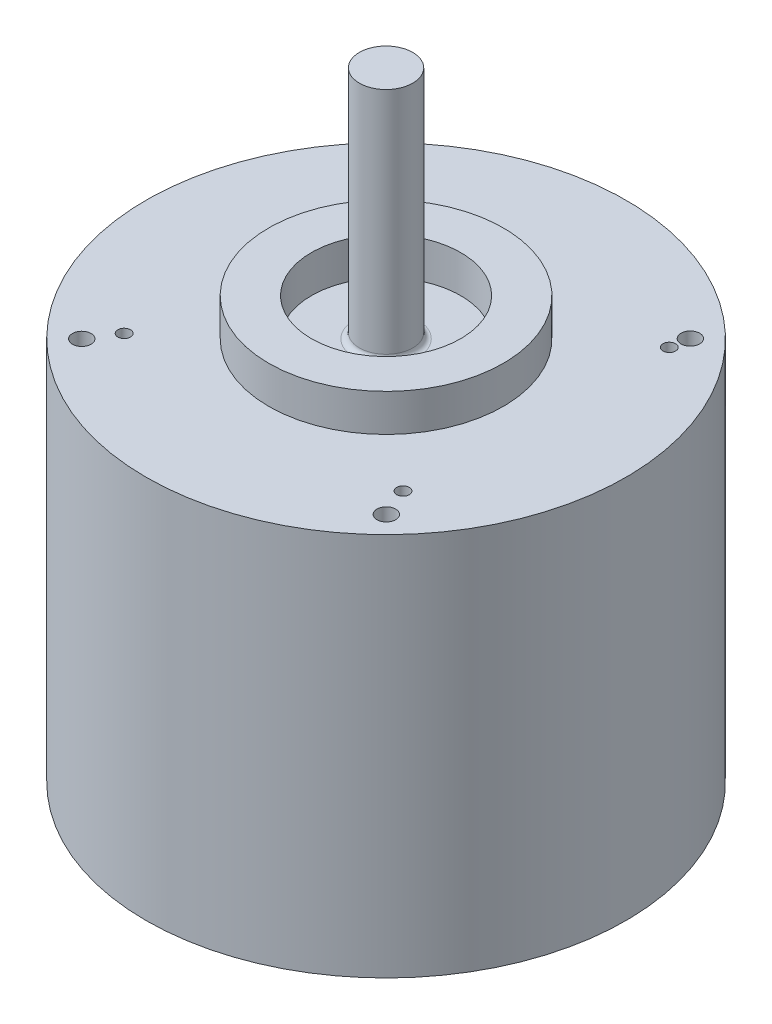
SolidWorks part; units mm, degrees
ref_plane "Front Plane" through (0, 0, 0) normal (0, 0, 1) x (1, 0, 0)
ref_plane "Top Plane" through (0, 0, 0) normal (0, 1, 0) x (1, 0, 0)
ref_plane "Right Plane" through (0, 0, 0) normal (1, 0, 0) x (0, 0, -1)
sketch "Sketch1" plane through (0, 0, 0) normal (0, 1, 0) x (1, 0, 0)
  circle A0 centre (0, 0) radius 22.5
  dimension "D1" = 45
extrude "Boss-Extrude1" add sketch "Sketch1" along normal blind 36
sketch "Sketch2" plane through (0, 36, 0) normal (0, 1, 0) x (1, 0, 0)
  circle A0 centre (0, 0) radius 11
extrude "Boss-Extrude2" add sketch "Sketch2" along normal blind 3.5
sketch "Sketch5" plane through (0, 39.5, 0) normal (0, 1, 0) x (1, 0, 0)
  circle A0 centre (0, 0) radius 7
extrude "Cut-Extrude1" cut sketch "Sketch5" against normal blind 3.5
sketch "Sketch6" plane through (0, 36, 0) normal (0, 1, 0) x (1, 0, 0)
  circle A0 centre (0, 0) radius 2.5
extrude "Boss-Extrude3" add sketch "Sketch6" along normal blind 22
fillet "Fillet1" radius 0.5 1 edges at (0, 36, 2.5)
sketch "Sketch7" plane through (0, 0, 0) normal (0, -1, 0) x (1, 0, 0)
  circle A1 centre (0, -11.5) radius 2.5
sketch "Sketch18" plane through (0, 36, 0) normal (0, 1, 0) x (1, 0, 0)
  line L1 (14.2767, -14.2534) -> (14.2534, 14.2767)
  line L2 (14.2534, 14.2767) -> (-14.2767, 14.2534)
  line L3 (-14.2767, 14.2534) -> (-14.2534, -14.2767)
  line L4 (-14.2534, -14.2767) -> (14.2767, -14.2534)
  circle A0 centre (0, 0) radius 14.265 construction
hole_wizard "M2.2x0.45 Tapped Hole1" positions "3DSketch6" profile "Sketch19" tap size "M2.2x0.45" standard "Ansi Metric"
sketch3d "3DSketch6"
  point P0 (-14.2767, 36, -14.2534)
  point P3 (14.2534, 36, -14.2767)
  point P6 (-14.2534, 36, 14.2767)
  point P9 (14.2767, 36, 14.2534)
sketch "Sketch19" plane through (-14.2767, 36, -14.2534) normal (1, 0, 0) x (0, 0, 1)
  line L0 (0, 0) -> (0, 6.2758)
  line L1 (0, 6.2758) -> (0.875, 5.75)
  line L2 (0.875, 5.75) -> (0.875, 0)
  line L5 (0.875, 0) -> (0, 0)
  line L10 (0, 6.2758) -> (-0.875, 5.75) construction
  line L11 (0, -6.35) -> (0, 107.95) construction
  dimension "Tap Drill Dia." = 1.75
  dimension "Tap Drill Depth" = 5.75
  dimension "Drill Angle" = 118
cosmetic thread "Hole Thread14" parameters "D1"=4.4, "D2"=2.2
cosmetic thread "Hole Thread15" parameters "D1"=4.4, "D2"=2.2
cosmetic thread "Hole Thread16" parameters "D1"=4.4, "D2"=2.2
cosmetic thread "Hole Thread17" parameters "D1"=4.4, "D2"=2.2
sketch "Sketch21" plane through (0, 0, 0) normal (0, -1, 0) x (1, 0, 0)
  circle A1 centre (0, -11.5) radius 2.4901
extrude "Boss-Extrude6" add sketch "Sketch21" along normal blind 7
hole_wizard "#0-80 Tapped Hole3" positions "3DSketch3" profile "Sketch14" tap size "#0-80" standard "Ansi Inch"
sketch3d "3DSketch3"
  point P0 (-13.1635, 36, -12.0288)
  point P2 (13.1635, 36, 11.5748)
  point P4 (13.9806, 36, -12.5735)
  point P6 (-12.7096, 36, 11.8472)
sketch "Sketch14" plane through (-13.1635, 36, -12.0288) normal (1, 0, 0) x (0, 0, 1)
  line L0 (0, 0) -> (0, 10.3579)
  line L1 (0, 10.3579) -> (0.5956, 10)
  line L2 (0.5956, 10) -> (0.5956, 0)
  line L5 (0.5956, 0) -> (0, 0)
  line L10 (0, 10.3579) -> (-0.5956, 10) construction
  line L11 (0, -6.35) -> (0, 107.95) construction
  dimension "Tap Drill Dia." = 1.1913
  dimension "Tap Drill Depth" = 10
  dimension "Drill Angle" = 118
cosmetic thread "Hole Thread6" parameters "D1"=4, "D2"=1.524
cosmetic thread "Hole Thread7" parameters "D1"=4, "D2"=1.524
cosmetic thread "Hole Thread8" parameters "D1"=4, "D2"=1.524
cosmetic thread "Hole Thread9" parameters "D1"=4, "D2"=1.524
sketch "Sketch17" plane through (0, 0, 0) normal (0, 1, 0) x (1, 0, 0)
  circle A0 centre (0, 11.5) radius 2.5
extrude "Boss-Extrude5" add sketch "Sketch17" against normal blind 6
